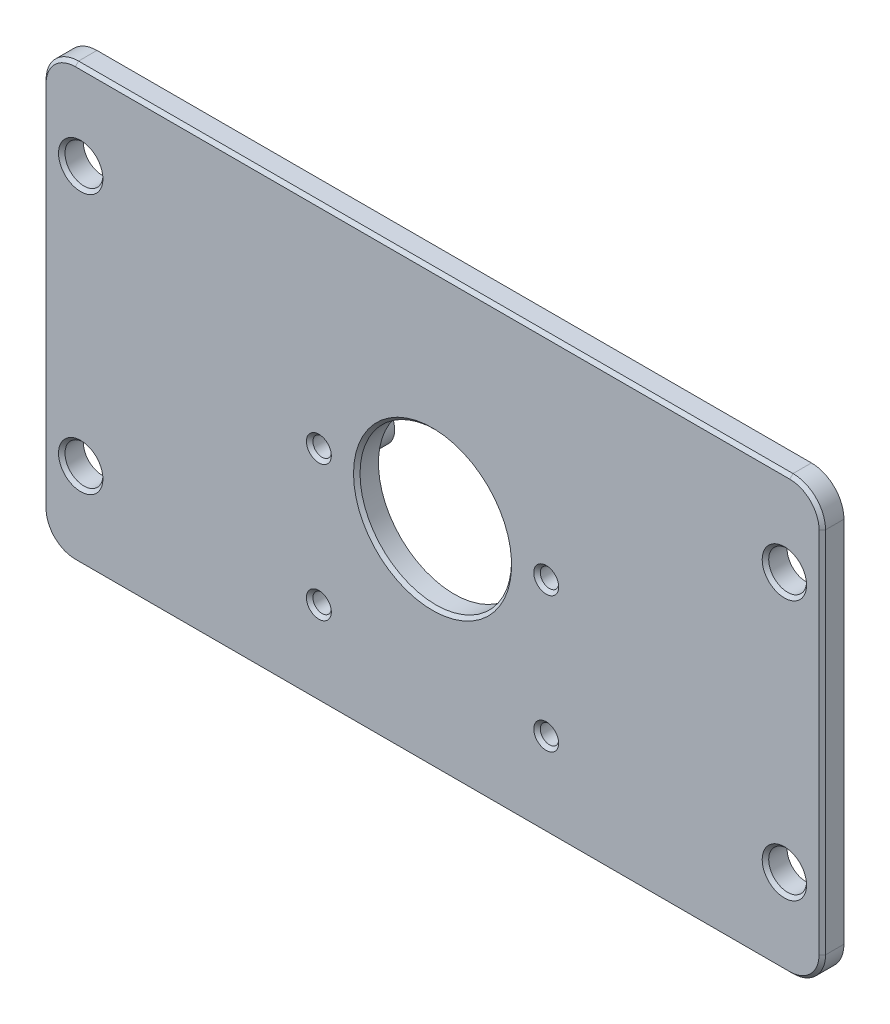
SolidWorks part; units mm, degrees
ref_plane "Спереди" through (0, 0, 0) normal (0, 0, 1) x (1, 0, 0)
ref_plane "Сверху" through (0, 0, 0) normal (0, 1, 0) x (1, 0, 0)
ref_plane "Справа" through (0, 0, 0) normal (1, 0, 0) x (0, 0, -1)
sketch "Эскиз1" plane through (0, 0, 0) normal (0, 0, 1) x (1, 0, 0)
  line L1 (-36, -20) -> (36, -20)
  line L2 (-36, -20) -> (-36, 20)
  line L3 (-36, 20) -> (36, 20)
  line L4 (36, -20) -> (36, 20)
  line L5 (-36, -20) -> (36, 20) construction
  line L6 (-36, 20) -> (36, -20) construction
  point P0 (0, 0)
  dimension "D1" = 72
  dimension "D2" = 40
extrude "Бобышка-Вытянуть1" add sketch "Эскиз1" along normal blind 2
sketch "Эскиз2" plane through (0, 0, 2) normal (0, 0, 1) x (1, 0, 0)
  circle A0 centre (0, 0) radius 7
  dimension "D1" = 14
extrude "Вырез-Вытянуть1" cut sketch "Эскиз2" against normal through all
fillet "Скругление1" radius 3 4 edges at (-36, 20, 1) (-36, -20, 1) (36, -20, 1) (36, 20, 1)
sketch "Эскиз5" plane through (0, 0, 2) normal (0, 0, 1) x (1, 0, 0)
  circle A1 centre (-32.5, -12) radius 1.75
  dimension "D1" = 12
  dimension "D6" = 3.5
  dimension "D2" = 32.5
extrude "Вырез-Вытянуть4" cut sketch "Эскиз5" against normal through all
pattern_linear "Линейный массив1" count 2 spacing 65 along (1, 0, 0) count 2 spacing 24 along (0, 1, 0) of "Вырез-Вытянуть4"
sketch "Эскиз7" plane through (0, 0, 0) normal (0, 0, -1) x (-1, 0, 0)
  circle A0 centre (-10.5, 0.4) radius 2
  circle A1 centre (-10.5, 0.4) radius 0.85
  point P2 (0, 0)
  point P5 (-22.0653, 6.4904)
  dimension "D1" = 4
  dimension "D3" = 1.7
  dimension "D2" = 10.5
  dimension "D4" = 0.4
extrude "Бобышка-Вытянуть2" add sketch "Эскиз7" along normal blind 3
sketch "Эскиз8" plane through (0, 0, 0) normal (0, 0, -1) x (-1, 0, 0)
  circle A0 centre (-10.5, 0.4) radius 0.85 construction
  circle A1 centre (-10.5, 0.4) radius 0.85
extrude "Вырез-Вытянуть6" cut sketch "Эскиз8" against normal blind 6
fillet "Скругление3" radius 1 1 edges at (8.5, 0.4, 0)
chamfer "Фаска1" distance 0.6 angle 45 1 edges at (9.65, 0.4, -3)
pattern_linear "Линейный массив2" count 2 spacing 12.5 along (0, -1, 0) count 2 spacing 21 along (-1, 0, 0) of "Бобышка-Вытянуть2", "Вырез-Вытянуть6", "Скругление3", "Фаска1"
chamfer "Фаска2" distance 0.3 angle 45 17 edges at (34.25, 12, 2) (-30.75, 12, 2) (35.1213, 19.1213, 2) (36, 0, 2) (35.1213, -19.1213, 2) (0, -20, 2) (-35.1213, -19.1213, 2) (-36, 0, 2) (-35.1213, 19.1213, 2) (0, 20, 2) (-30.75, -12, 2) (34.25, -12, 2) (9.65, 0.4, 2) (-11.35, -12.1, 2) (9.65, -12.1, 2) (-11.35, 0.4, 2) (7, 0, 2)
